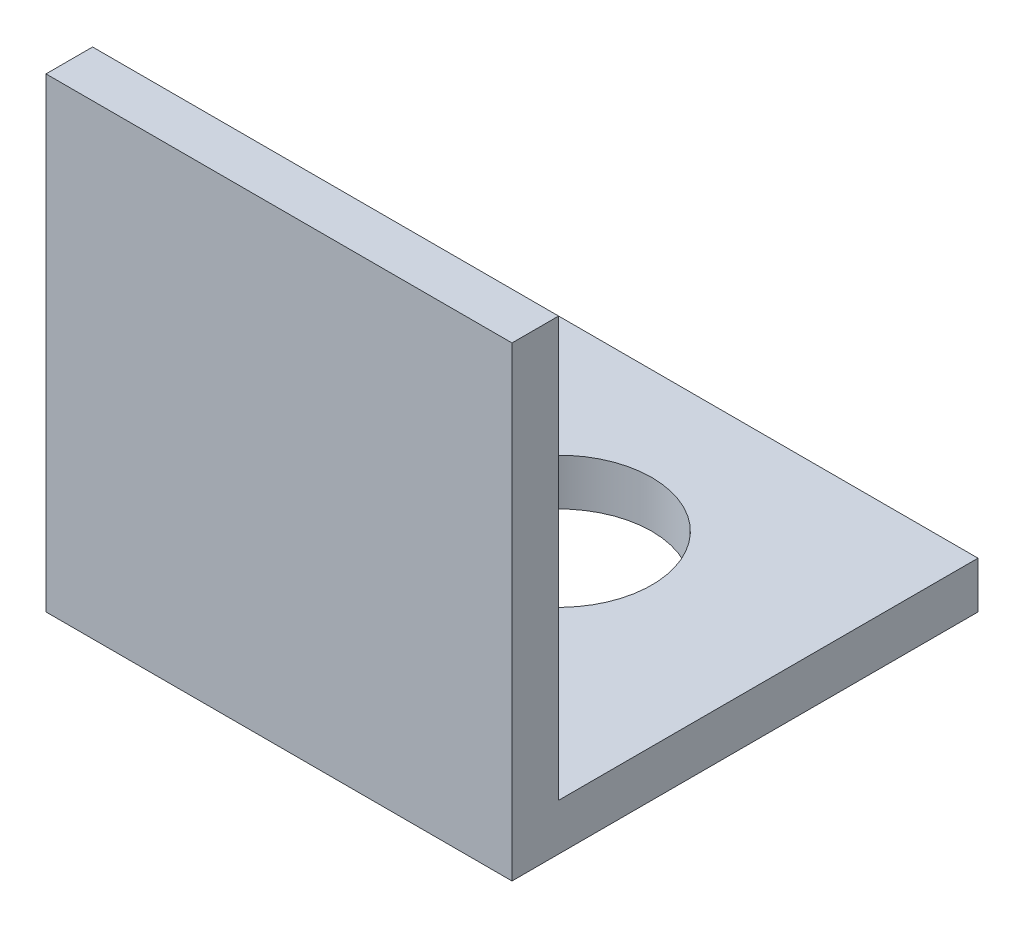
SolidWorks part; units mm, degrees
ref_plane "Спереди" through (0, 0, 0) normal (0, 0, 1) x (1, 0, 0)
ref_plane "Сверху" through (0, 0, 0) normal (0, 1, 0) x (1, 0, 0)
ref_plane "Справа" through (0, 0, 0) normal (1, 0, 0) x (0, 0, -1)
sketch "Эскиз1" plane through (0, 0, 0) normal (1, 0, 0) x (0, 0, -1)
  line L0 (0, 30) -> (0, 0)
  line L1 (0, 0) -> (30, 0)
extrude "Вытянуть-Тонкостенный1" add sketch "Эскиз1" along normal blind 30 thin thin type one direction reverse wall 3
sketch "Эскиз2" plane through (0, 0, 0) normal (0, -1, 0) x (1, 0, 0)
  circle A0 centre (15, -18) radius 6
extrude "Вырез-Вытянуть1" cut sketch "Эскиз2" against normal through all
